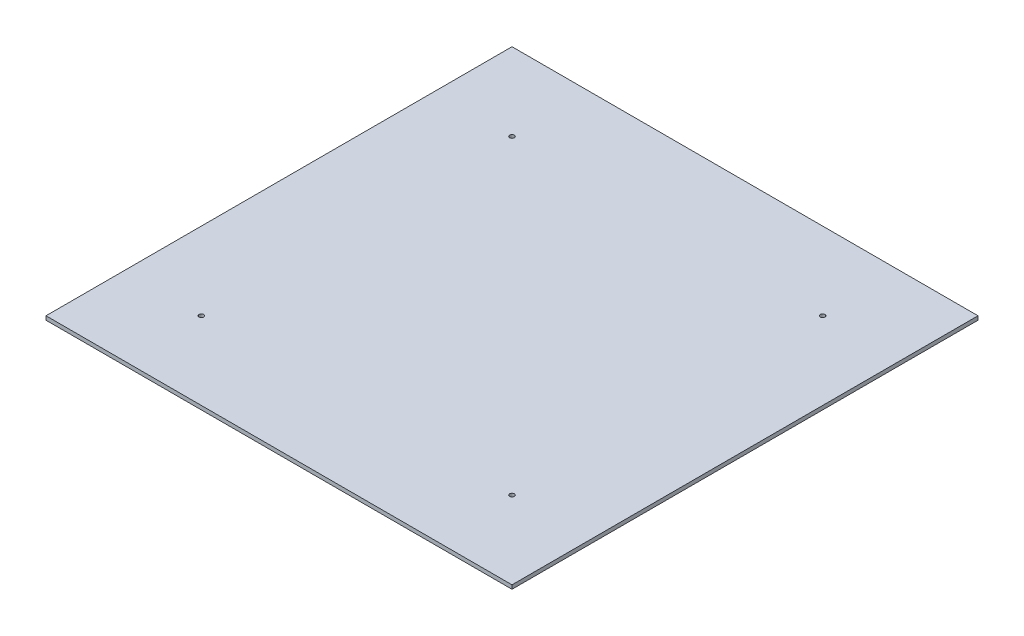
SolidWorks part; units mm, degrees
material "Plain Carbon Steel"
ref_plane "Front Plane" through (0, 0, 0) normal (0, 0, 1) x (1, 0, 0)
ref_plane "Top Plane" through (0, 0, 0) normal (0, 1, 0) x (1, 0, 0)
ref_plane "Right Plane" through (0, 0, 0) normal (1, 0, 0) x (0, 0, -1)
sketch "Sketch1" plane through (0, 0, 0) normal (0, 1, 0) x (1, 0, 0)
  line L0 (-150, 0) -> (0, 0) construction
  line L1 (-150, 150) -> (150, 150)
  line L2 (-150, 150) -> (-150, -150)
  line L3 (-150, -150) -> (150, -150)
  line L4 (150, 150) -> (150, -150)
  line L5 (-150, 150) -> (150, -150) construction
  line L6 (-150, -150) -> (150, 150) construction
  line L7 (0, 0) -> (0, 150) construction
  circle A0 centre (-100, 100) radius 1.5
  circle A1 centre (100, 100) radius 1.5
  circle A2 centre (-100, -100) radius 1.5
  circle A3 centre (100, -100) radius 1.5
  point P0 (0, 0)
  point P10 (-105.1529, 105.1529)
  dimension "D2" = 3
  dimension "D1" = 300
  dimension "D3" = 50
extrude "Boss-Extrude1" add sketch "Sketch1" along normal blind 2.5
